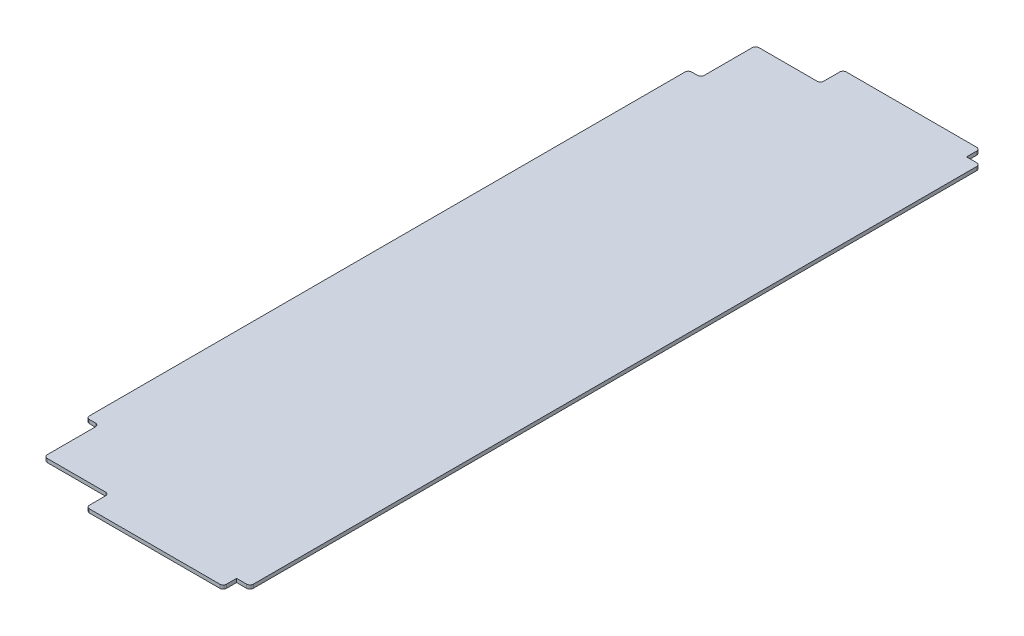
SolidWorks part; units mm, degrees
ref_plane "Front Plane" through (0, 0, 0) normal (0, 0, 1) x (1, 0, 0)
ref_plane "Top Plane" through (0, 0, 0) normal (0, 1, 0) x (1, 0, 0)
ref_plane "Right Plane" through (0, 0, 0) normal (1, 0, 0) x (0, 0, -1)
sketch "Sketch1" plane through (0, 0, 0) normal (0, 1, 0) x (1, 0, 0)
  line L1 (0, 0) -> (190.5, 0)
  line L2 (0, 0) -> (0, 609.6)
  line L3 (0, 609.6) -> (190.5, 609.6)
  line L4 (190.5, 0) -> (190.5, 609.6)
  dimension "D1" = 609.6
  dimension "D2" = 190.5
extrude "Boss-Extrude1" add sketch "Sketch1" along normal blind 2.7781
sketch "Sketch2" plane through (0, 2.7781, 0) normal (0, 1, 0) x (1, 0, 0)
  line L0 (190.5, 0) -> (190.5, 609.6) construction
  line L1 (0, 0) -> (190.5, 0)
  line L2 (0, 0) -> (0, 17.78)
  line L3 (0, 17.78) -> (190.5, 17.78)
  line L4 (190.5, 0) -> (190.5, 17.78)
  line L6 (0, 609.6) -> (190.5, 609.6)
  line L7 (0, 609.6) -> (0, 591.82)
  line L8 (0, 591.82) -> (190.5, 591.82)
  line L9 (190.5, 609.6) -> (190.5, 591.82)
  dimension "D1" = 17.78
  dimension "D2" = 17.78
extrude "Cut-Extrude1" cut sketch "Sketch2" against normal through all
sketch "Sketch3" plane through (0, 2.7781, 0) normal (0, 1, 0) x (1, 0, 0)
  line L0 (190.5, 17.78) -> (0, 17.78) construction
  line L1 (0, 591.82) -> (17.78, 591.82)
  line L2 (0, 591.82) -> (0, 17.78)
  line L3 (0, 17.78) -> (17.78, 17.78)
  line L4 (17.78, 591.82) -> (17.78, 17.78)
  dimension "D1" = 17.78
extrude "Cut-Extrude2" cut sketch "Sketch3" against normal through all
sketch "Sketch4" plane through (0, 2.7781, 0) normal (0, 1, 0) x (1, 0, 0)
  line L0 (17.78, 591.82) -> (76.454, 591.82)
  line L1 (17.78, 591.82) -> (190.5, 591.82) construction
  line L2 (76.454, 591.82) -> (76.454, 574.675)
  line L3 (76.454, 574.675) -> (27.305, 574.675)
  line L4 (27.305, 574.675) -> (27.305, 533.146)
  line L5 (27.305, 533.146) -> (17.78, 533.146)
  line L6 (17.78, 17.78) -> (17.78, 591.82) construction
  line L7 (17.78, 533.146) -> (17.78, 591.82)
  line L8 (17.78, 17.78) -> (76.454, 17.78)
  line L9 (190.5, 17.78) -> (17.78, 17.78) construction
  line L10 (76.454, 17.78) -> (76.454, 34.925)
  line L11 (76.454, 34.925) -> (27.305, 34.925)
  line L12 (27.305, 34.925) -> (27.305, 76.454)
  line L13 (27.305, 76.454) -> (17.78, 76.454)
  line L14 (17.78, 76.454) -> (17.78, 17.78)
  line L16 (190.5, 591.82) -> (180.34, 591.82)
  line L17 (190.5, 591.82) -> (190.5, 581.66)
  line L18 (190.5, 581.66) -> (180.34, 581.66)
  line L19 (180.34, 591.82) -> (180.34, 581.66)
  line L20 (190.5, 17.78) -> (180.34, 17.78)
  line L21 (190.5, 17.78) -> (190.5, 27.94)
  line L22 (190.5, 27.94) -> (180.34, 27.94)
  line L23 (180.34, 17.78) -> (180.34, 27.94)
  dimension "D1" = 9.525
  dimension "D2" = 58.674
  dimension "D3" = 17.145
  dimension "D4" = 10.16
extrude "Cut-Extrude3" cut sketch "Sketch4" against normal through all
fillet "Fillet1" radius 2.54 14 edges at (76.454, 1.3891, -17.78) (76.454, 1.3891, -34.925) (27.305, 1.3891, -34.925) (27.305, 1.3891, -76.454) (17.78, 1.3891, -76.454) (17.78, 1.3891, -533.146) (76.454, 1.3891, -591.82) (76.454, 1.3891, -574.675) (27.305, 1.3891, -574.675) (180.34, 1.3891, -591.82) (190.5, 1.3891, -581.66) (190.5, 1.3891, -27.94) (180.34, 1.3891, -17.78) (27.305, 1.3891, -533.146)
